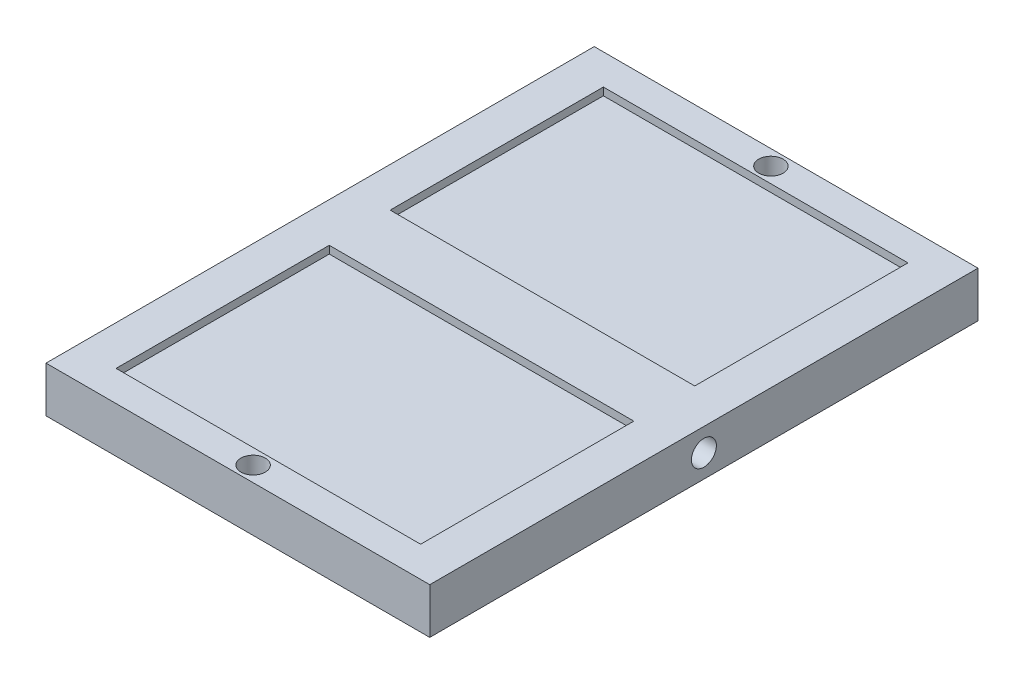
SolidWorks part; units mm, degrees
ref_plane "Front Plane" through (0, 0, 0) normal (0, 0, 1) x (1, 0, 0)
ref_plane "Top Plane" through (0, 0, 0) normal (0, 1, 0) x (1, 0, 0)
ref_plane "Right Plane" through (0, 0, 0) normal (1, 0, 0) x (0, 0, -1)
sketch "Sketch1" plane through (0, 0, 0) normal (0, 1, 0) x (1, 0, 0)
  line L1 (63, 90) -> (-63, 90)
  line L2 (63, 90) -> (63, -90)
  line L3 (63, -90) -> (-63, -90)
  line L4 (-63, 90) -> (-63, -90)
  line L5 (63, 90) -> (-63, -90) construction
  line L6 (63, -90) -> (-63, 90) construction
  point P0 (0, 0)
  dimension "D1" = 180
  dimension "D2" = 126
extrude "Boss-Extrude1" add sketch "Sketch1" along normal blind 15
sketch "Sketch2" plane through (0, 15, 0) normal (0, 1, 0) x (1, 0, 0)
  line L0 (-63, -90) -> (63, -90) construction
  line L1 (-50, -10) -> (50, -10)
  line L2 (-50, -10) -> (-50, -80)
  line L3 (-50, -80) -> (50, -80)
  line L4 (50, -10) -> (50, -80)
  line L5 (63, -90) -> (63, 90) construction
  line L6 (-55, 0) -> (55, 0) construction
  line L7 (-50, 10) -> (-50, 80)
  line L8 (-50, 80) -> (50, 80)
  line L9 (50, 10) -> (50, 80)
  line L10 (-50, 10) -> (50, 10)
  dimension "D1" = 70
  dimension "D2" = 100
  dimension "D3" = 10
  dimension "D4" = 13
extrude "Cut-Extrude1" cut sketch "Sketch2" against normal blind 2.5
sketch "Sketch4" plane through (0, 0, 0) normal (0, 1, 0) x (1, 0, 0)
  line L0 (0, -55) -> (0, 55) construction
  line L1 (-63, -90) -> (63, -90) construction
  line L2 (-55, 0) -> (55, 0) construction
  circle A0 centre (0, -85) radius 4
  circle A1 centre (0, 85) radius 4
  dimension "D1" = 8
  dimension "D2" = 5
extrude "Cut-Extrude3" cut sketch "Sketch4" along normal blind 32.5
sketch "Sketch5" plane through (0, 0, 0) normal (1, 0, 0) x (0, 0, -1)
  line L0 (0, 8.25) -> (0, -8.25) construction
  line L1 (-90, 0) -> (90, 0) construction
  circle A0 centre (0, 7.5) radius 4.1
  dimension "D1" = 8.2
  dimension "D2" = 7.5
extrude "Cut-Extrude4" cut sketch "Sketch5" against normal through all and the other way through all contours A0
